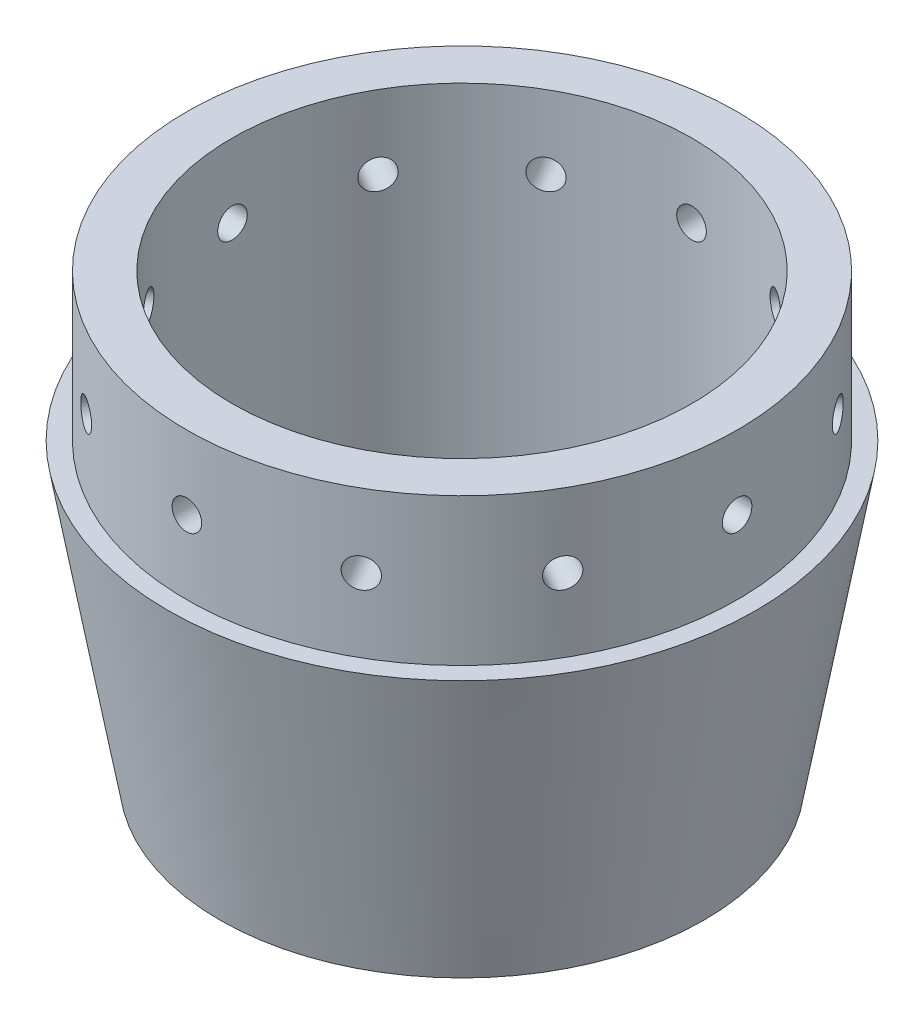
SolidWorks part; units mm, degrees
material "6061-T6 (SS)"
ref_plane "Front Plane" through (0, 0, 0) normal (0, 0, 1) x (1, 0, 0)
ref_plane "Top Plane" through (0, 0, 0) normal (0, 1, 0) x (1, 0, 0)
ref_plane "Right Plane" through (0, 0, 0) normal (1, 0, 0) x (0, 0, -1)
sketch "Sketch1" plane through (0, 0, 0) normal (0, 0, 1) x (1, 0, 0)
  line L0 (-39.7256, 0) -> (-41.8426, 0)
  line L1 (-41.8426, 0) -> (-50.8, 50.8)
  line L2 (-50.8, 50.8) -> (-47.5869, 50.8)
  line L3 (-47.5869, 50.8) -> (-47.5869, 76.2)
  line L4 (-47.5869, 76.2) -> (-39.7256, 76.2)
  line L5 (-39.7256, 76.2) -> (-39.7256, 0)
  line L6 (0, 0) -> (0, 80.0677) construction
  line L7 (-39.7256, 0) -> (0, 0) construction
  point P2 (0, 0)
  dimension "D1" = 10
  dimension "D2" = 50.8
  dimension "D3" = 25.4
  dimension "D4" = 39.7256
  dimension "D5" = 50.8
  dimension "D6" = 47.5869
revolve "Revolve1" add sketch "Sketch1" angle 360 about L6
ref_plane "Plane1" through (0, 0, -47.5869) normal (0, 0, -1) x (-1, 0, 0)
sketch "Sketch2" plane through (0, 0, -47.5869) normal (0, 0, -1) x (-1, 0, 0)
  line L0 (47.5869, 76.2) -> (-47.5869, 76.2) construction
  point P0 (0, 63.5)
  point P3 (0, 0)
  dimension "D1" = 12.7
hole_wizard "Tap Drill for 1/4-20 Tap1" positions "Sketch3" profile "Sketch4" hole size "1/4-20" standard "ANSI Inch"
sketch "Sketch3" plane through (0, 0, -47.5869) normal (0, 0, -1) x (-1, 0, 0)
  point P0 (0, 63.5)
sketch "Sketch4" plane through (0, 63.5, -47.5869) normal (1, 0, 0) x (0, 1, 0)
  line L0 (0, 0) -> (0, 7.8613)
  line L1 (0, 7.8613) -> (2.5527, 7.8613)
  line L2 (2.5527, 7.8613) -> (2.5527, 0)
  line L5 (2.5527, 0) -> (0, 0)
  line L11 (0, -6.35) -> (0, 107.95) construction
  dimension "Thru Hole Dia." = 5.1054
  dimension "Thru Hole Depth" = 7.8613
pattern_circular "CirPattern1" count 12 over 360 about axis through (0, 0, 0) along (0, -1, 0) of "Tap Drill for 1/4-20 Tap1"
